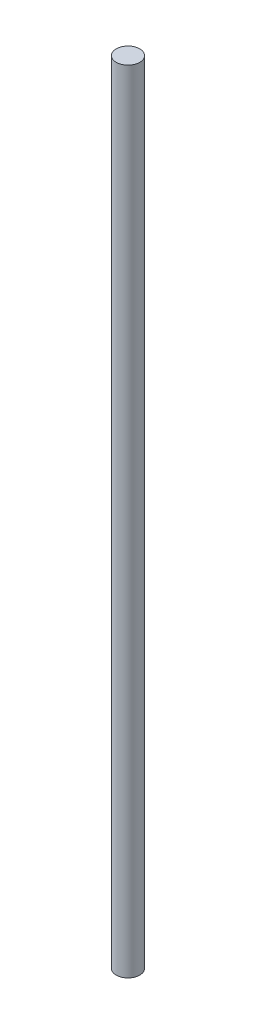
SolidWorks part; units mm, degrees
ref_plane "前视基准面" through (0, 0, 0) normal (0, 0, 1) x (1, 0, 0)
ref_plane "上视基准面" through (0, 0, 0) normal (0, 1, 0) x (1, 0, 0)
ref_plane "右视基准面" through (0, 0, 0) normal (1, 0, 0) x (0, 0, -1)
sketch "草图1" plane through (0, 0, 0) normal (0, 1, 0) x (1, 0, 0)
  circle A0 centre (0, 0) radius 4
  dimension "D1" = 8
extrude "凸台-拉伸1" add sketch "草图1" along normal blind 270
